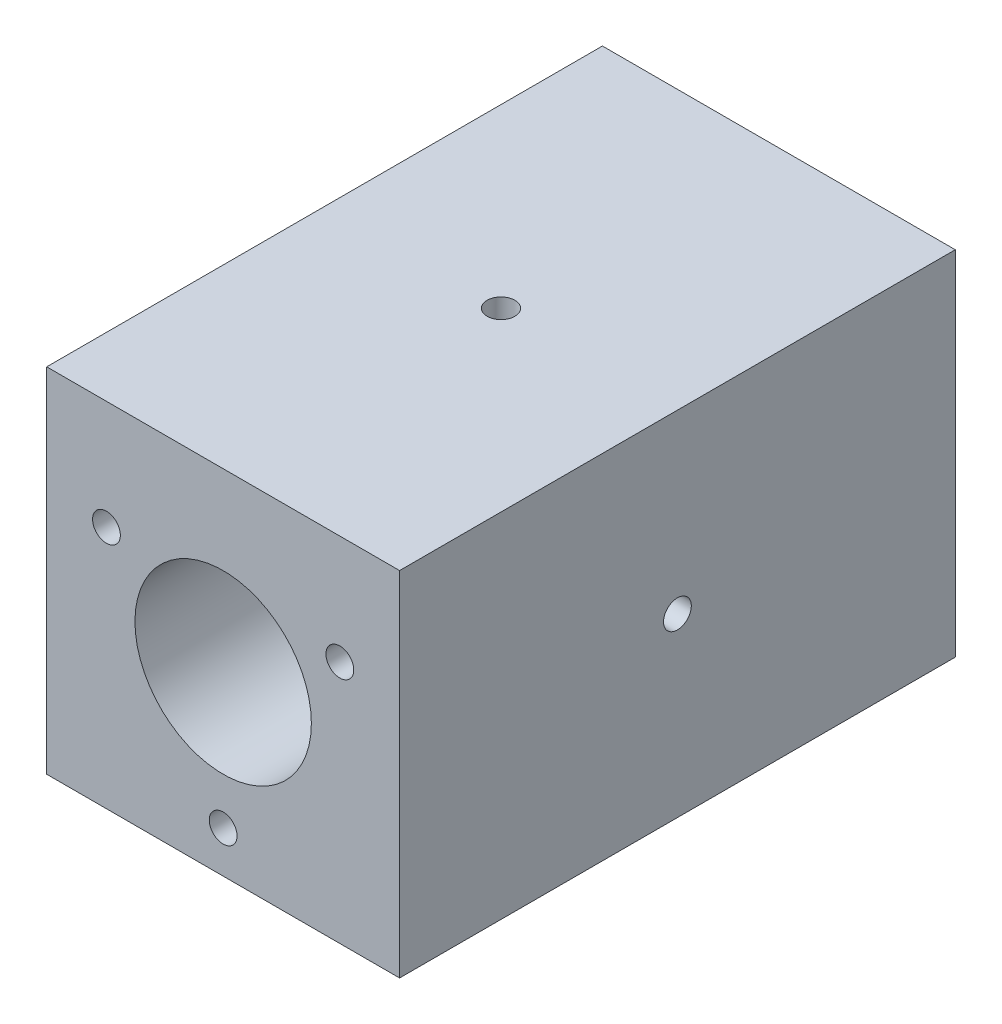
SolidWorks part; units mm, degrees
material "6061-T6 (SS)"
ref_plane "Front Plane" through (0, 0, 0) normal (0, 0, 1) x (1, 0, 0)
ref_plane "Top Plane" through (0, 0, 0) normal (0, 1, 0) x (1, 0, 0)
ref_plane "Right Plane" through (0, 0, 0) normal (1, 0, 0) x (0, 0, -1)
sketch "Sketch1" plane through (0, 0, 0) normal (0, 0, 1) x (1, 0, 0)
  line L1 (15.875, 15.875) -> (-15.875, 15.875)
  line L2 (15.875, 15.875) -> (15.875, -15.875)
  line L3 (15.875, -15.875) -> (-15.875, -15.875)
  line L4 (-15.875, 15.875) -> (-15.875, -15.875)
  line L5 (15.875, 15.875) -> (-15.875, -15.875) construction
  line L6 (15.875, -15.875) -> (-15.875, 15.875) construction
  circle A0 centre (0, 0) radius 7.9375
  circle A1 centre (-10.5, 6.0622) radius 1.25
  circle A2 centre (10.5, 6.0622) radius 1.25
  circle A3 centre (0, -12.1244) radius 1.25
  point P0 (0, 0)
  point P16 (0, 0)
  dimension "D2" = 15.875
  dimension "D3" = 2.5
  dimension "D1" = 31.75
  dimension "D5" = 21
  dimension "D4" = 3
extrude "Boss-Extrude1" add sketch "Sketch1" along normal mid plane 50
hole_wizard "M3x0.5 Tapped Hole1" positions "Sketch2" profile "Sketch3" tap size "M3x0.5" standard "ANSI Metric"
sketch "Sketch2" plane through (0, 15.875, 0) normal (0, 1, 0) x (1, 0, 0)
  point P0 (0, 0)
sketch "Sketch3" plane through (0, 15.875, 0) normal (1, 0, 0) x (0, 0, 1)
  line L0 (0, 0) -> (0, 7.9375)
  line L1 (0, 7.9375) -> (1.25, 7.9375)
  line L2 (1.25, 7.9375) -> (1.25, 0)
  line L5 (1.25, 0) -> (0, 0)
  line L11 (0, -6.35) -> (0, 107.95) construction
  dimension "Thru Tap Drill Dia." = 2.5
  dimension "Thru Tap Drill Depth" = 7.9375
cosmetic thread "Hole Thread1" parameters "D2"=3
hole_wizard "M3x0.5 Tapped Hole2" positions "Sketch4" profile "Sketch5" tap size "M3x0.5" standard "ANSI Metric"
sketch "Sketch4" plane through (15.875, 0, 0) normal (1, 0, 0) x (0, 0, -1)
  point P0 (0, 0)
sketch "Sketch5" plane through (15.875, 0, 0) normal (0, 1, 0) x (0, 0, -1)
  line L0 (0, 0) -> (0, 7.9375)
  line L1 (0, 7.9375) -> (1.25, 7.9375)
  line L2 (1.25, 7.9375) -> (1.25, 0)
  line L5 (1.25, 0) -> (0, 0)
  line L11 (0, -6.35) -> (0, 107.95) construction
  dimension "Thru Tap Drill Dia." = 2.5
  dimension "Thru Tap Drill Depth" = 7.9375
cosmetic thread "Hole Thread2" parameters "D2"=3
